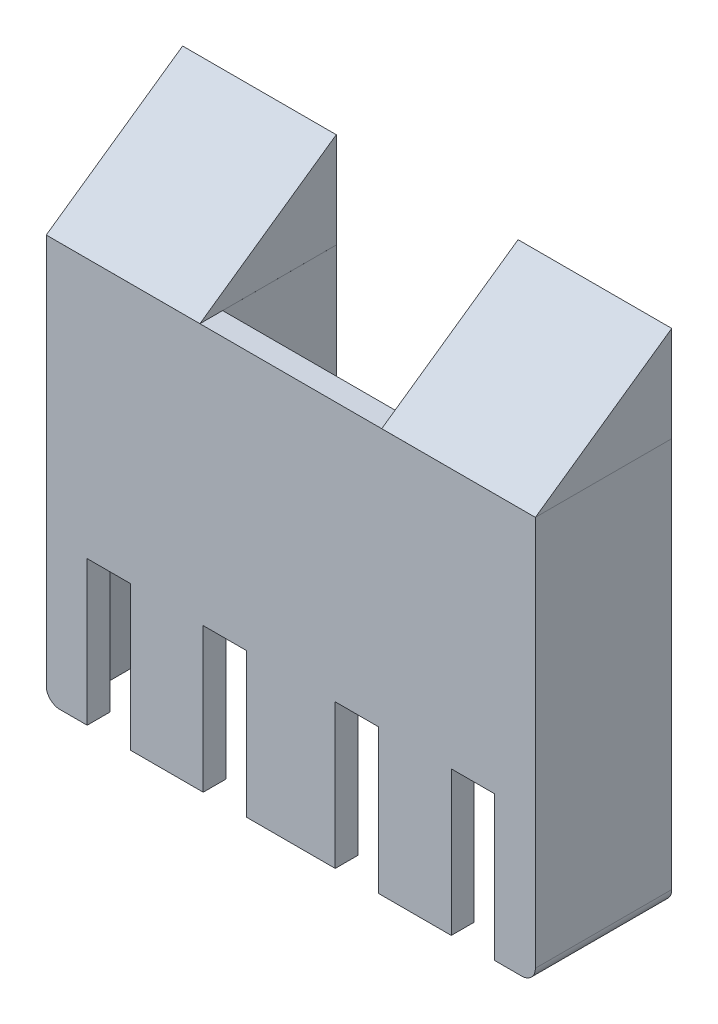
SolidWorks part; units mm, degrees
ref_plane "Front Plane" through (0, 0, 0) normal (0, 0, 1) x (1, 0, 0)
ref_plane "Top Plane" through (0, 0, 0) normal (0, 1, 0) x (1, 0, 0)
ref_plane "Right Plane" through (0, 0, 0) normal (1, 0, 0) x (0, 0, -1)
sketch "Sketch4" plane through (0, 0, 0) normal (0, 0, 1) x (1, 0, 0)
  line L1 (-50.8, -44.45) -> (50.8, -44.45)
  line L2 (-50.8, -44.45) -> (-50.8, 44.45)
  line L3 (-50.8, 44.45) -> (50.8, 44.45)
  line L4 (50.8, -44.45) -> (50.8, 44.45)
  line L5 (-50.8, -44.45) -> (50.8, 44.45) construction
  line L6 (-50.8, 44.45) -> (50.8, -44.45) construction
  point P0 (0, 0)
  dimension "D1" = 88.9
  dimension "D2" = 101.6
extrude "Boss-Extrude3" add sketch "Sketch4" along normal blind 30
sketch "Sketch7" plane through (0, 0, 25) normal (0, 0, -1) x (-1, 0, 0)
  line L0 (50.8, -44.45) -> (50.8, 44.45) construction
  line L5 (-50.8, -44.45) -> (50.8, -44.45) construction
  line L6 (35.3, -12.7) -> (44.8, -12.7)
  line L7 (35.3, -12.7) -> (35.3, -44.45)
  line L8 (35.3, -44.45) -> (44.8, -44.45)
  line L9 (44.8, -12.7) -> (44.8, -44.45)
  line L10 (35.3, -12.7) -> (44.8, -44.45) construction
  line L11 (35.3, -44.45) -> (44.8, -12.7) construction
  line L16 (-50.8, -44.45) -> (-50.8, 44.45) construction
  line L17 (-44.8, -12.7) -> (-35.3, -12.7)
  line L18 (-44.8, -12.7) -> (-44.8, -44.45)
  line L19 (-44.8, -44.45) -> (-35.3, -44.45)
  line L20 (-35.3, -12.7) -> (-35.3, -44.45)
  line L21 (-44.8, -12.7) -> (-35.3, -44.45) construction
  line L22 (-44.8, -44.45) -> (-35.3, -12.7) construction
  line L23 (-19.27, -12.7) -> (-9.77, -12.7)
  line L24 (9.77, -12.7) -> (19.27, -12.7)
  line L25 (9.77, -12.7) -> (9.77, -44.45)
  line L26 (9.77, -44.45) -> (19.27, -44.45)
  line L27 (19.27, -12.7) -> (19.27, -44.45)
  line L28 (9.77, -12.7) -> (19.27, -44.45) construction
  line L29 (9.77, -44.45) -> (19.27, -12.7) construction
  line L30 (-19.27, -12.7) -> (-19.27, -44.45)
  line L31 (-19.27, -44.45) -> (-9.77, -44.45)
  line L32 (-9.77, -12.7) -> (-9.77, -44.45)
  point P0 (40.05, -28.575)
  point P10 (-40.05, -28.575)
  point P16 (14.52, -28.575)
  dimension "D1" = 31.75
  dimension "D2" = 9.5
  dimension "D3" = 6
  dimension "D4" = 6
  dimension "D5" = 25.53
  dimension "D6" = 25.53
extrude "Cut-Extrude5" cut sketch "Sketch7" against normal through all both and the other way through all
sketch "Sketch8" plane through (0, 0, 0) normal (0, 0, -1) x (-1, 0, 0)
  line L0 (-50.8, -44.45) -> (-44.8208, -12.8098)
  line L1 (-20, 44.45) -> (20, 44.45)
  line L2 (-50.8, 44.45) -> (50.8, 44.45) construction
  line L3 (-20, 44.45) -> (-44.7555, -12.5975)
  line L4 (50.8, -44.45) -> (44.8573, -13.0032)
  line L5 (44.8, -44.45) -> (44.8, -12.7) construction
  line L6 (44.5818, -12.4818) -> (24.3934, 7.7066)
  line L7 (20, 18.3132) -> (20, 44.45)
  line L8 (-50.8, -44.45) -> (50.8, -44.45)
  arc A0 (24.3934, 7.7066) -> (20, 18.3132) centre (35, 18.3132) cw
  arc A1 (44.8573, -13.0032) -> (44.5818, -12.4818) centre (43.8747, -13.1889) ccw
  arc A2 (-44.8208, -12.8098) -> (-44.7555, -12.5975) centre (-43.8381, -12.9955) cw
  point P9 (0, 44.45)
  point P25 (44.8, -12.7)
  point P28 (-44.8, -12.7)
  dimension "D3" = 15
  dimension "D4" = 1
  dimension "D5" = 1
  dimension "D1" = 40
  dimension "D2" = 135
extrude "Cut-Extrude6" cut sketch "Sketch8" against normal blind 25 and the other way through all
sketch "Sketch9" plane through (0, 0, 30) normal (0, 0, 1) x (1, 0, 0)
  line L0 (50.8, -44.45) -> (50.8, 44.45) construction
  line L2 (53.8, -41.4525) -> (53.8, 44.4525)
  line L5 (52.8359, -43.6559) -> (-53.8, 44.4525) construction
  line L6 (53.8, 44.4525) -> (-53.8, -44.4525) construction
  line L7 (0, 0) -> (0, 44.4525) construction
  line L8 (-53.8, -41.4525) -> (-53.8, 44.4525)
  line L9 (50.8, -44.4525) -> (50.8, 44.4525)
  line L11 (-50.8, 44.45) -> (-50.8, -44.4525)
  line L12 (53.8, 44.4525) -> (50.8, 44.4525)
  line L13 (-53.8, 44.4525) -> (-50.8, 44.45)
  arc A0 (50.8, -44.4525) -> (53.8, -41.4525) centre (50.8, -41.4525) ccw
  arc A1 (-50.8, -44.4525) -> (-53.8, -41.4525) centre (-50.8, -41.4525) cw
  point P0 (0, 0)
  dimension "D1" = 3
extrude "Boss-Extrude4" add sketch "Sketch9" against normal blind 30
sketch "Sketch10" plane through (-53.8, 0, 0) normal (-1, 0, 0) x (0, 0, 1)
  line L0 (0, 44.4525) -> (0, 65.4588)
  line L1 (0, 65.4588) -> (30, 44.4525)
  line L2 (30, 44.4525) -> (0, 44.4525)
  dimension "D1" = 35
extrude "Boss-Extrude6" add sketch "Sketch10" against normal blind 107.6 separate body
sketch "Sketch11" plane through (0, 0, 0) normal (0, 0, -1) x (-1, 0, 0)
  line L0 (20, 44.45) -> (20, 65.4588)
  line L1 (-53.8, 65.4588) -> (53.8, 65.4588) construction
  line L2 (-20, 44.45) -> (-20, 65.4588)
  line L3 (-20, 65.4588) -> (20, 65.4588)
  line L4 (-20, 44.45) -> (20, 44.45)
  line L6 (-53.8, 44.4525) -> (53.8, 44.4525) construction
  point P8 (0, 0)
  point P9 (-20, 44.45)
extrude "Cut-Extrude10" cut sketch "Sketch11" against normal through all both and the other way through all
